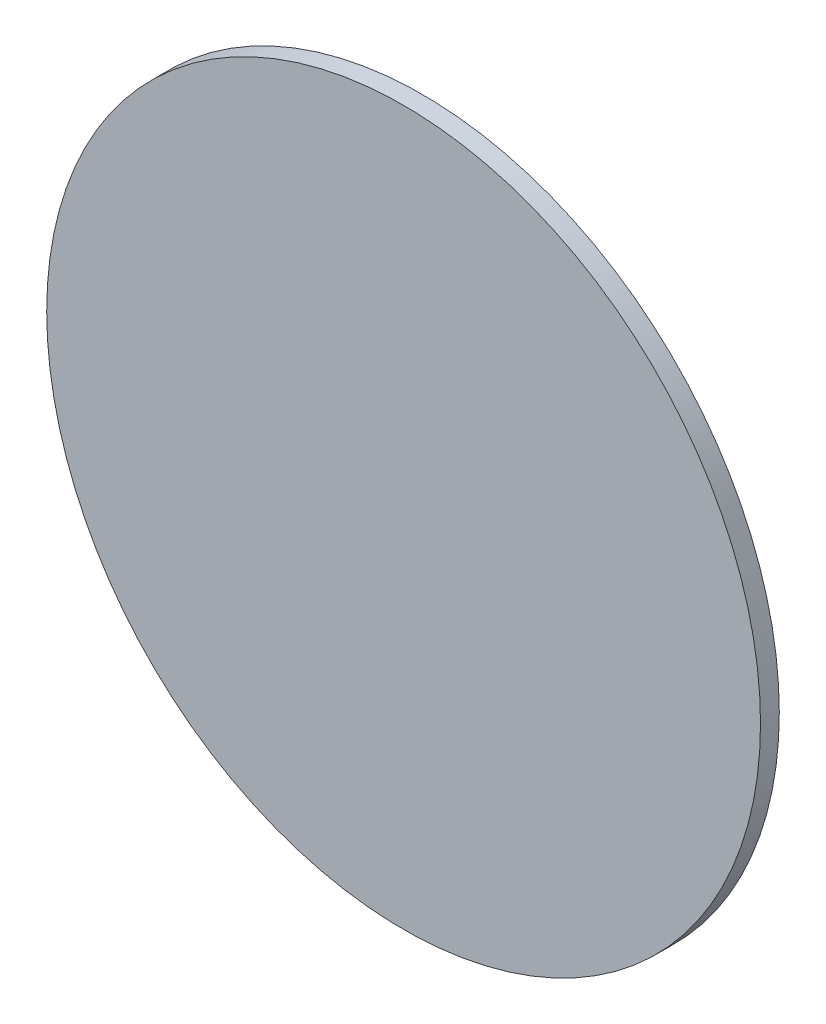
SolidWorks part; units mm, degrees
ref_plane "Front Plane" through (0, 0, 0) normal (0, 0, 1) x (1, 0, 0)
ref_plane "Top Plane" through (0, 0, 0) normal (0, 1, 0) x (1, 0, 0)
ref_plane "Right Plane" through (0, 0, 0) normal (1, 0, 0) x (0, 0, -1)
sketch "Croquis2" plane through (0, 0, 0) normal (0, 0, 1) x (1, 0, 0)
  circle A0 centre (0, 0) radius 19
  dimension "D1" = 38
extrude "Saliente-Extruir1" add sketch "Croquis2" along normal blind 1
